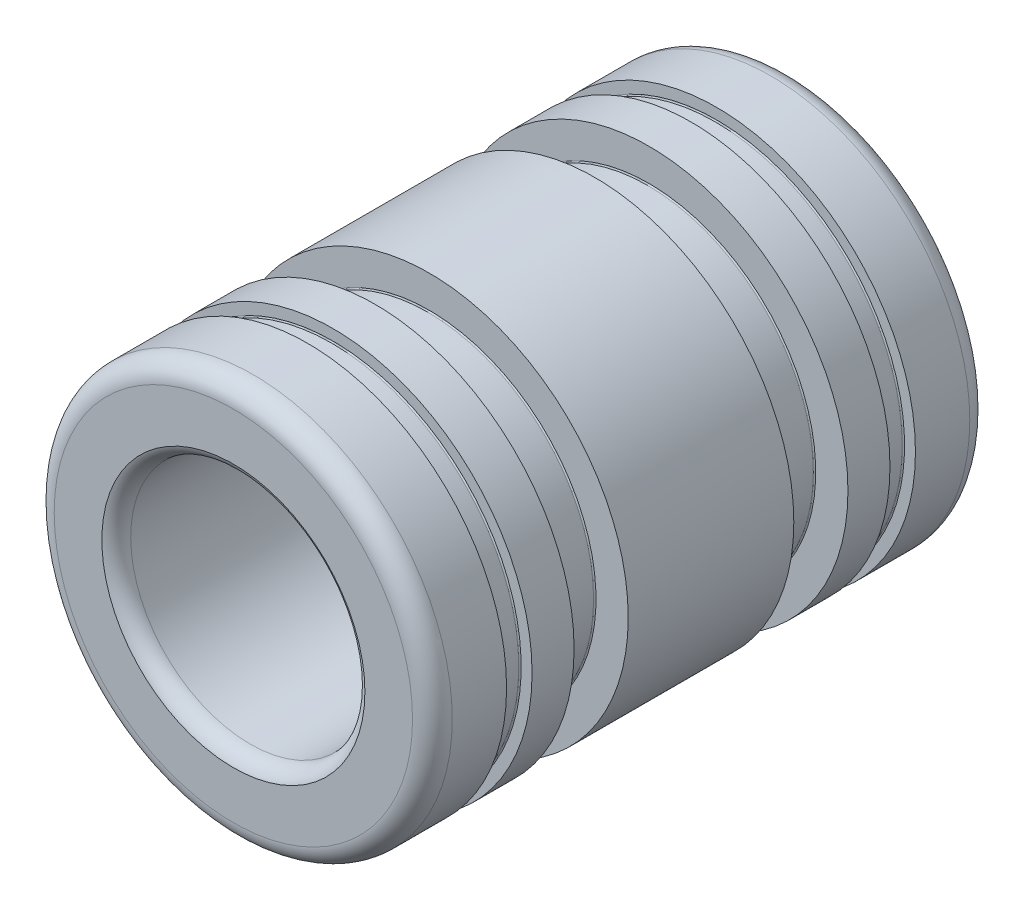
SolidWorks part; units mm, degrees
ref_plane "Front Plane" through (0, 0, 0) normal (0, 0, 1) x (1, 0, 0)
ref_plane "Top Plane" through (0, 0, 0) normal (0, 1, 0) x (1, 0, 0)
ref_plane "Right Plane" through (0, 0, 0) normal (1, 0, 0) x (0, 0, -1)
sketch "Sketch1" plane through (0, 0, 0) normal (0, 0, 1) x (1, 0, 0)
  circle A0 centre (0, 0) radius 4.7688
  circle A1 centre (0, 0) radius 7.9375
  dimension "ID" = 9.5377
  dimension "OD" = 15.875
sketch "Sketch2" plane through (0, 0, 0) normal (1, 0, 0) x (0, 0, -1)
  line L0 (-11.1125, 7.9375) -> (11.1125, 7.9375) construction
  line L1 (-11.1125, 0) -> (11.1125, 0) construction
  line L4 (-8.1534, 7.4549) -> (-7.1374, 7.4549)
  line L6 (0, 4.7688) -> (0, -4.7688) construction
  line L10 (-5.461, 6.604) -> (-3.302, 6.604)
  line L11 (-8.1534, 7.4549) -> (-8.1534, -7.4549) construction
  line L12 (-7.1374, 7.4549) -> (-7.1374, -7.4549) construction
  line L13 (-5.461, 6.604) -> (-5.461, -6.604) construction
  line L14 (-3.302, 6.604) -> (-3.302, -6.604) construction
  line L15 (11.1125, 4.7625) -> (11.1125, -4.7625) construction
  line L16 (-11.1125, 7.9375) -> (-11.1125, -7.9375) construction
  line L17 (11.1125, 7.9375) -> (11.1125, 7.8867) construction
  line L18 (0, 0) -> (11.1125, 0.194) construction
  line L19 (0, 0) -> (11.1125, -0.194) construction
  point P4 (0, 7.9375)
  point P9 (-8.1534, 0)
  point P20 (-5.461, 0)
  point P30 (8.1534, -7.4549)
  point P32 (-8.1534, -7.4549)
  dimension "Overall Length" = 22.225
  dimension "Retaining Ring Groove Width" = 1.016
  dimension "Retaining Ring Groove OD" = 14.9098
  dimension "Retaining Ring Groove End-to-End Length" = 16.3068
  dimension "O-ring Groove Width" = 2.159
  dimension "O-ring Groove Gap" = 6.604
  dimension "O-ring Groove OD" = 13.208
  dimension "For Shaft Diameter" = 9.525
  dimension "Housing Finish Thickness" = 0.0508
  dimension "Misalignment Capability" = 2
  dimension "Half Misalignment" = 1
sketch "Sketch3" plane through (0, 0, 0) normal (1, 0, 0) x (0, 0, -1)
  line L0 (-11.1125, 7.9375) -> (-8.1534, 7.9375)
  line L1 (-11.1125, 7.9375) -> (11.1125, 7.9375) construction
  line L2 (-8.1534, 7.9375) -> (-8.1534, 7.4549)
  line L3 (-8.1534, 7.4549) -> (-7.1374, 7.4549)
  line L4 (-7.1374, 7.4549) -> (-7.1374, 7.9375)
  line L5 (-7.1374, 7.9375) -> (-5.461, 7.9375)
  line L6 (-5.461, 7.9375) -> (-5.461, 6.604)
  line L7 (-5.461, 6.604) -> (-3.302, 6.604)
  line L8 (-3.302, 6.604) -> (-3.302, 7.9375)
  line L9 (-3.302, 7.9375) -> (3.302, 7.9375)
  line L10 (-11.1125, 7.9375) -> (-11.1125, 5.2457)
  line L11 (-11.1125, 5.2457) -> (11.1125, 5.2457)
  line L12 (0, 5.2457) -> (0, 7.9375) construction
  line L13 (3.302, 6.604) -> (3.302, 7.9375)
  line L14 (5.461, 6.604) -> (3.302, 6.604)
  line L15 (5.461, 7.9375) -> (5.461, 6.604)
  line L16 (7.1374, 7.9375) -> (5.461, 7.9375)
  line L17 (7.1374, 7.4549) -> (7.1374, 7.9375)
  line L18 (8.1534, 7.4549) -> (7.1374, 7.4549)
  line L19 (8.1534, 7.9375) -> (8.1534, 7.4549)
  line L20 (11.1125, 7.9375) -> (8.1534, 7.9375)
  line L21 (11.1125, 7.9375) -> (11.1125, 5.2457)
  line L22 (0, 0) -> (-3.302, 0) construction
  line L23 (-3.302, 6.604) -> (-3.302, -6.604) construction
  dimension "D1" = 10.4915
revolve "Revolve1" add sketch "Sketch3" angle 360 about L1
fillet "Fillet1" radius 0.7922 2 edges at (7.9375, 0, -11.1125) (7.9375, 0, 11.1125)
fillet "Fillet2" radius 0.0483 8 edges at (6.604, 0, 3.302) (6.604, 0, 5.461) (6.604, 0, -5.461) (6.604, 0, -3.302) (7.4549, 0, -8.1534) (7.4549, 0, -7.1374) (7.4549, 0, 7.1374) (7.4549, 0, 8.1534)
sketch "Sketch4" plane through (0, 0, 0) normal (1, 0, 0) x (0, 0, -1)
  line L1 (0, 5.2457) -> (0, 4.7688) construction
  line L2 (10.4381, 4.7689) -> (-10.4381, 4.7688)
  line L3 (-11.1125, 5.2457) -> (0, 5.2457)
  line L5 (11.1125, 5.2457) -> (0, 5.2457)
  line L6 (-11.1125, 7.9375) -> (-11.1125, -7.9375) construction
  arc A0 (-10.4381, 4.7688) -> (-11.1125, 5.2457) centre (-10.4381, 5.4842) cw
  arc A1 (10.4381, 4.7689) -> (11.1125, 5.2457) centre (10.4381, 5.4842) ccw
  dimension "D2" = 0.7153
revolve "Revolve2" add sketch "Sketch4" angle 360 about L1
equation "\"D1@Sketch3\"=\"ID@Sketch1\"*1.1"
equation "\"D1@Fillet1\" =  ( \"OD@Sketch1\" - \"ID@Sketch1\" )  * .5 * .25"
equation "\"D2@Sketch4\"=\"ID@Sketch1\"*.075"
equation "\"Half Misalignment@Sketch2\"=\"Misalignment Capability@Sketch2\"*.5"
equation "\"D1@Fillet2\"=( \"OD@Sketch1\" - \"Retaining Ring Groove OD@Sketch2\" )  * .5 * .1"
